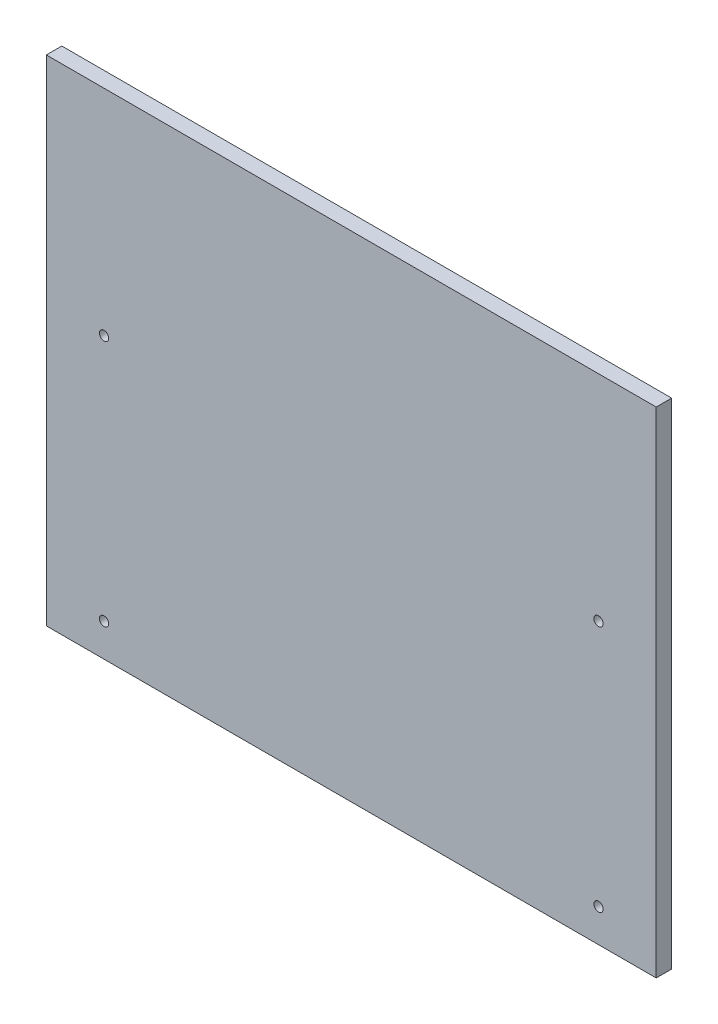
SolidWorks part; units mm, degrees
material "Pine"
ref_plane "Front Plane" through (0, 0, 0) normal (0, 0, 1) x (1, 0, 0)
ref_plane "Top Plane" through (0, 0, 0) normal (0, 1, 0) x (1, 0, 0)
ref_plane "Right Plane" through (0, 0, 0) normal (1, 0, 0) x (0, 0, -1)
sketch "Sketch1" plane through (0, 0, 0) normal (0, 0, 1) x (1, 0, 0)
  line L1 (-234.95, -190.5) -> (234.95, -190.5)
  line L2 (-234.95, -190.5) -> (-234.95, 190.5)
  line L3 (-234.95, 190.5) -> (234.95, 190.5)
  line L4 (234.95, -190.5) -> (234.95, 190.5)
  line L5 (-234.95, -190.5) -> (234.95, 190.5) construction
  line L6 (-234.95, 190.5) -> (234.95, -190.5) construction
  point P0 (0, 0)
  dimension "D1" = 469.9
  dimension "D2" = 381
extrude "Boss-Extrude1" add sketch "Sketch1" along normal blind 11.9062
sketch "Sketch2" plane through (0, 0, 11.9062) normal (0, 0, 1) x (1, 0, 0)
  line L0 (-234.95, -190.5) -> (234.95, -190.5) construction
  line L1 (234.95, 190.5) -> (-234.95, 190.5) construction
  point P0 (-190.5, -165.1)
  point P1 (190.5, -165.1)
  point P2 (190.5, 25.4)
  point P3 (-190.5, 25.4)
  point P7 (117.475, 171.45)
  point P9 (-117.475, 171.45)
  dimension "D1" = 381
  dimension "D2" = 190.5
  dimension "D3" = 25.4
  dimension "D4" = 190.5
  dimension "D5" = 234.95
  dimension "D6" = 117.475
  dimension "D7" = 19.05
hole_wizard "9/32 (0.28125) Diameter Hole1" positions "3DSketch1" profile "Sketch3" hole size "9/32" standard "ANSI Inch" end condition through all
sketch3d "3DSketch1"
  point P0 (-190.5, 25.4, 11.9062)
  point P3 (190.5, 25.4, 11.9062)
  point P6 (190.5, -165.1, 11.9062)
  point P9 (-190.5, -165.1, 11.9062)
sketch "Sketch3" plane through (-190.5, 25.4, 11.9062) normal (1, 0, 0) x (0, -1, 0)
  line L0 (0, 0) -> (0, 11.9062)
  line L1 (0, 11.9062) -> (3.5719, 11.9062)
  line L2 (3.5719, 11.9062) -> (3.5719, 0)
  line L5 (3.5719, 0) -> (0, 0)
  line L11 (0, -6.35) -> (0, 107.95) construction
  dimension "Thru Hole Dia." = 7.1437
  dimension "Thru Hole Depth" = 11.9062
